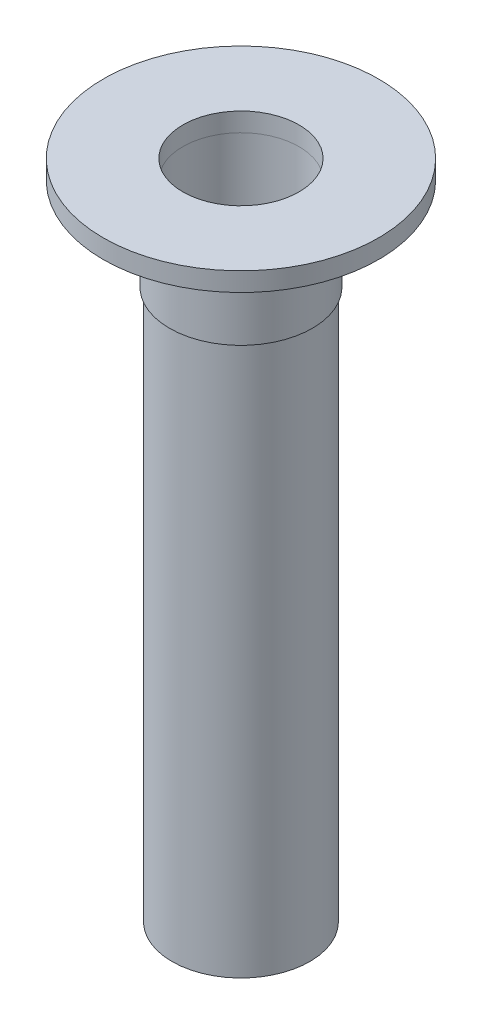
SolidWorks part; units mm, degrees
ref_plane "Front Plane" through (0, 0, 0) normal (0, 0, 1) x (1, 0, 0)
ref_plane "Top Plane" through (0, 0, 0) normal (0, 1, 0) x (1, 0, 0)
ref_plane "Right Plane" through (0, 0, 0) normal (1, 0, 0) x (0, 0, -1)
sketch "Sketch1" plane through (0, 0, 0) normal (0, 0, 1) x (1, 0, 0)
  line L0 (0, 20.7229) -> (0, -44.9471)
  line L1 (0, 20.7229) -> (-13.675, 20.7229)
  line L2 (-13.675, 20.7229) -> (-13.675, 18.8529)
  line L3 (-13.675, 18.8529) -> (-7.095, 18.8529)
  line L4 (-7.095, 18.8529) -> (-7.095, 9.6529)
  line L5 (-7.095, 9.6529) -> (-6.845, 9.6529)
  line L6 (-6.845, 9.6529) -> (-6.845, -44.9471)
  line L7 (-6.845, -44.9471) -> (0, -44.9471)
  dimension "D1" = 13.675
  dimension "D4" = 1.87
  dimension "D5" = 9.2
  dimension "D6" = 54.6
revolve "Revolve1" add sketch "Sketch1" angle 360 about L0
sketch "Sketch2" plane through (0, 20.7229, 0) normal (0, 1, 0) x (1, 0, 0)
  circle A0 centre (0, 0) radius 5.77
extrude "Cut-Extrude1" cut sketch "Sketch2" against normal blind 1.87
sketch "Sketch3" plane through (0, 18.8529, 0) normal (0, 1, 0) x (1, 0, 0)
  circle A0 centre (0, 0) radius 5.785
extrude "Cut-Extrude2" cut sketch "Sketch3" against normal blind 9.2
sketch "Sketch4" plane through (0, 9.6529, 0) normal (0, 1, 0) x (1, 0, 0)
  circle A0 centre (0, 0) radius 5.675
extrude "Cut-Extrude3" cut sketch "Sketch4" against normal blind 54.6
